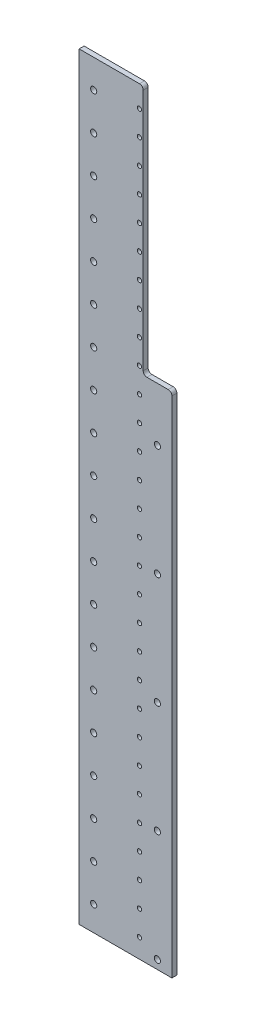
SolidWorks part; units mm, degrees
ref_plane "前视基准面" through (0, 0, 0) normal (0, 0, 1) x (1, 0, 0)
ref_plane "上视基准面" through (0, 0, 0) normal (0, 1, 0) x (1, 0, 0)
ref_plane "右视基准面" through (0, 0, 0) normal (1, 0, 0) x (0, 0, -1)
sketch "草图2" plane through (0, 0, 0) normal (0, 0, 1) x (1, 0, 0)
  line L0 (0, 0) -> (75, 0)
  line L1 (75, 0) -> (75, -613)
  line L2 (75, -613) -> (0, -613)
  line L3 (0, -613) -> (0, 0)
extrude "凸台-拉伸1" add sketch "草图2" along normal blind 4
sketch "草图3" plane through (0, 0, 0) normal (0, 0, -1) x (-1, 0, 0)
  circle A0 centre (-48.0768, -587.0519) radius 1.75
  circle A2 centre (-48.0768, -567.0519) radius 1.75
  circle A3 centre (-48.0768, -547.0519) radius 1.75
  circle A4 centre (-48.0768, -527.0519) radius 1.75
  circle A5 centre (-48.0768, -507.0519) radius 1.75
  circle A6 centre (-48.0768, -487.0519) radius 1.75
  circle A7 centre (-48.0768, -467.0519) radius 1.75
  circle A8 centre (-48.0768, -447.0519) radius 1.75
  circle A9 centre (-48.0768, -427.0519) radius 1.75
  circle A10 centre (-48.0768, -407.0519) radius 1.75
  circle A11 centre (-48.0768, -387.0519) radius 1.75
  circle A12 centre (-48.0768, -367.0519) radius 1.75
  circle A13 centre (-48.0768, -347.0519) radius 1.75
  circle A14 centre (-48.0768, -327.0519) radius 1.75
  circle A15 centre (-48.0768, -307.0519) radius 1.75
  circle A16 centre (-48.0768, -287.0519) radius 1.75
  circle A17 centre (-48.0768, -267.0519) radius 1.75
  circle A18 centre (-48.0768, -247.0519) radius 1.75
  circle A19 centre (-48.0768, -227.0519) radius 1.75
  circle A20 centre (-48.0768, -207.0519) radius 1.75
  circle A21 centre (-48.0768, -187.0519) radius 1.75
  circle A22 centre (-48.0768, -167.0519) radius 1.75
  circle A23 centre (-48.0768, -147.0519) radius 1.75
  circle A24 centre (-48.0768, -127.0519) radius 1.75
  circle A25 centre (-48.0768, -107.0519) radius 1.75
  circle A26 centre (-48.0768, -87.0519) radius 1.75
  circle A27 centre (-48.0768, -67.0519) radius 1.75
  circle A28 centre (-48.0768, -47.0519) radius 1.75
  circle A29 centre (-48.0768, -27.0519) radius 1.75
  circle A30 centre (-48.0768, -7.0519) radius 1.75
  dimension "D1" = 3.5
  dimension "D2" = 3.5
  dimension "D3" = 3.5
  dimension "D4" = 1.75
  dimension "D5" = 1.75
  dimension "D6" = 1.75
  dimension "D7" = 1.75
  dimension "D8" = 1.75
  dimension "D9" = 1.75
  dimension "D10" = 1.75
  dimension "D11" = 1.75
  dimension "D12" = 1.75
  dimension "D13" = 1.75
  dimension "D14" = 1.75
  dimension "D15" = 1.75
  dimension "D16" = 1.75
  dimension "D17" = 1.75
  dimension "D18" = 1.75
  dimension "D19" = 1.75
  dimension "D20" = 1.75
  dimension "D21" = 1.75
  dimension "D22" = 1.75
  dimension "D23" = 1.75
  dimension "D24" = 1.75
  dimension "D25" = 1.75
  dimension "D26" = 1.75
  dimension "D27" = 1.75
  dimension "D28" = 1.75
  dimension "D29" = 1.75
  dimension "D30" = 1.75
sketch "草图7" plane through (0, 0, 0) normal (0, 0, -1) x (-1, 0, 0)
  line L0 (-75, 0) -> (-51.8029, 0)
  line L1 (-75, 0) -> (0, 0) construction
  line L2 (-51.8029, 0) -> (-51.8029, -202.5155)
  line L3 (-51.8029, -202.5155) -> (-75, -202.5155)
  line L4 (-75, -613) -> (-75, 0) construction
  line L5 (-75, -202.5155) -> (-75, 0)
extrude "切除-拉伸2" cut sketch "草图7" against normal through all
fillet "圆角1" radius 3 3 edges at (75, -202.5155, 2) (51.8029, -202.5155, 2) (51.8029, 0, 2)
sketch "草图8" plane through (0, 0, 0) normal (0, 0, -1) x (-1, 0, 0)
  circle A0 centre (-48.75, -17.5) radius 1.75
  circle A1 centre (-48.75, -37.5) radius 1.75
  circle A2 centre (-48.75, -57.5) radius 1.75
  circle A3 centre (-48.75, -77.5) radius 1.75
  circle A4 centre (-48.75, -97.5) radius 1.75
  circle A5 centre (-48.75, -117.5) radius 1.75
  circle A6 centre (-48.75, -137.5) radius 1.75
  circle A7 centre (-48.75, -157.5) radius 1.75
  circle A8 centre (-48.75, -177.5) radius 1.75
  circle A9 centre (-48.75, -197.5) radius 1.75
  circle A10 centre (-48.75, -217.5) radius 1.75
  circle A11 centre (-48.75, -237.5) radius 1.75
  circle A12 centre (-48.75, -257.5) radius 1.75
  circle A13 centre (-48.75, -277.5) radius 1.75
  circle A14 centre (-48.75, -297.5) radius 1.75
  circle A15 centre (-48.75, -317.5) radius 1.75
  circle A16 centre (-48.75, -337.5) radius 1.75
  circle A17 centre (-48.75, -357.5) radius 1.75
  circle A18 centre (-48.75, -377.5) radius 1.75
  circle A19 centre (-48.75, -397.5) radius 1.75
  circle A20 centre (-48.75, -417.5) radius 1.75
  circle A21 centre (-48.75, -437.5) radius 1.75
  circle A22 centre (-48.75, -457.5) radius 1.75
  circle A23 centre (-48.75, -477.5) radius 1.75
  circle A24 centre (-48.75, -497.5) radius 1.75
  circle A25 centre (-48.75, -517.5) radius 1.75
  circle A26 centre (-48.75, -537.5) radius 1.75
  circle A27 centre (-48.75, -557.5) radius 1.75
  circle A28 centre (-48.75, -577.5) radius 1.75
  circle A29 centre (-48.75, -597.5) radius 1.75
  dimension "D1" = 3.5
  dimension "D2" = 30
extrude "切除-拉伸3" cut sketch "草图8" against normal through all
sketch "草图9" plane through (0, 0, 4) normal (0, 0, 1) x (1, 0, 0)
  line L0 (3.25, -613) -> (20.25, -613) construction
  line L1 (0, -613) -> (75, -613) construction
  line L2 (3.25, -643.5525) -> (3.25, 31.5547) construction
  line L3 (20.25, -643.5525) -> (20.25, 31.5547) construction
  line L4 (11.75, -613) -> (11.75, -593) construction
  circle A0 centre (11.75, -593) radius 2.5
  circle A1 centre (11.75, -563) radius 2.5
  circle A2 centre (11.75, -533) radius 2.5
  circle A3 centre (11.75, -503) radius 2.5
  circle A4 centre (11.75, -473) radius 2.5
  circle A5 centre (11.75, -443) radius 2.5
  circle A6 centre (11.75, -413) radius 2.5
  circle A7 centre (11.75, -383) radius 2.5
  circle A8 centre (11.75, -353) radius 2.5
  circle A9 centre (11.75, -323) radius 2.5
  circle A10 centre (11.75, -293) radius 2.5
  circle A11 centre (11.75, -263) radius 2.5
  circle A12 centre (11.75, -233) radius 2.5
  circle A13 centre (11.75, -203) radius 2.5
  circle A14 centre (11.75, -173) radius 2.5
  circle A15 centre (11.75, -143) radius 2.5
  circle A16 centre (11.75, -113) radius 2.5
  circle A17 centre (11.75, -83) radius 2.5
  circle A18 centre (11.75, -53) radius 2.5
  circle A19 centre (11.75, -23) radius 2.5
  dimension "D1" = 5
  dimension "D2" = 20
extrude "切除-拉伸4" cut sketch "草图9" against normal through all
sketch "草图10" plane through (0, 0, 4) normal (0, 0, 1) x (1, 0, 0)
  line L0 (54.75, -613) -> (71.75, -613) construction
  line L1 (0, -613) -> (75, -613) construction
  line L2 (54.75, 117.3104) -> (54.75, -682.6896) construction
  line L3 (71.75, 117.3104) -> (71.75, -682.6896) construction
  line L4 (63.25, -613) -> (63.25, -605.9506) construction
  circle A0 centre (63.25, -605.9506) radius 2.5
  circle A1 centre (63.25, -515.9506) radius 2.5
  circle A2 centre (63.25, -425.9506) radius 2.5
  circle A3 centre (63.25, -335.9506) radius 2.5
  circle A4 centre (63.25, -245.9506) radius 2.5
  dimension "D1" = 5
  dimension "D2" = 5
extrude "切除-拉伸5" cut sketch "草图10" against normal through all
